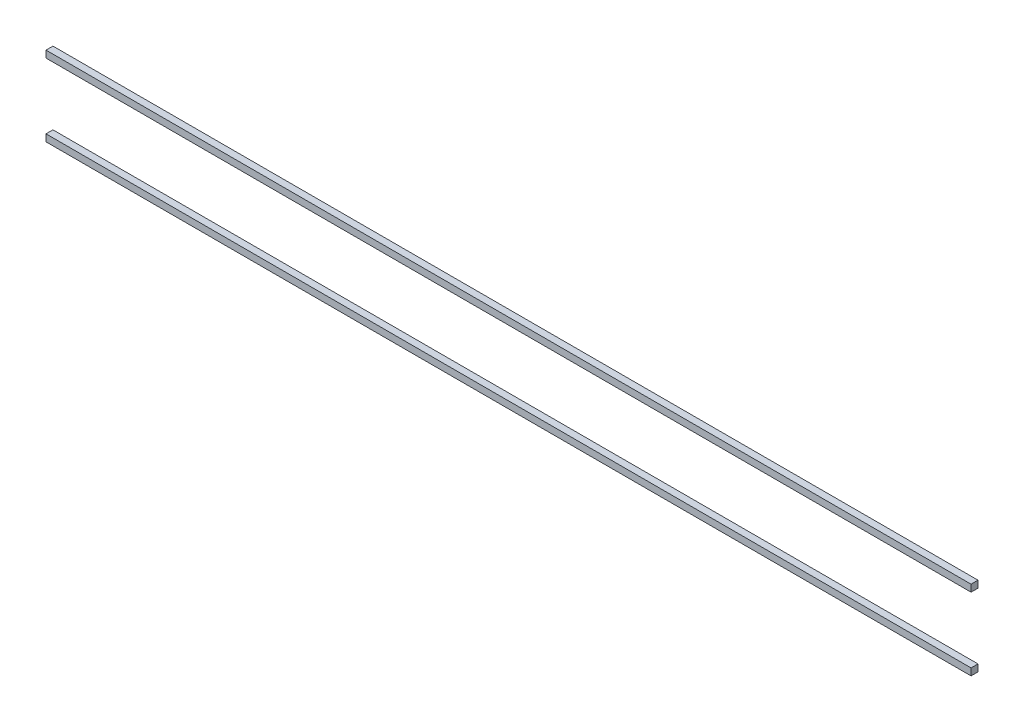
SolidWorks part; units mm, degrees
material "Balsa"
ref_plane "Front Plane" through (0, 0, 0) normal (0, 0, 1) x (1, 0, 0)
ref_plane "Top Plane" through (0, 0, 0) normal (0, 1, 0) x (1, 0, 0)
ref_plane "Right Plane" through (0, 0, 0) normal (1, 0, 0) x (0, 0, -1)
sketch "Sketch1" plane through (0, 0, 0) normal (0, 0, 1) x (1, 0, 0)
  line L0 (-18.175, 48.175) -> (18.175, 48.175)
  line L4 (405, 11.825) -> (405, 15)
  line L5 (-15, 45) -> (15, 45)
  line L7 (-15, 15) -> (15, 15)
  line L10 (405, 11.825) -> (405, 15)
  line L14 (-18.175, 11.825) -> (18.175, 11.825)
  line L16 (18.175, 48.175) -> (405, 48.175)
  line L17 (18.175, 11.825) -> (405, 11.825)
  line L18 (15, 45) -> (405, 45)
  line L19 (15, 15) -> (405, 15)
  line L20 (-18.175, 48.175) -> (-18.175, 45)
  line L21 (-18.175, 48.175) -> (-18.175, 11.825) construction
  line L22 (-15, 45) -> (-15, 15) construction
  line L23 (15, 45) -> (15, 15) construction
  line L24 (-18.175, 45) -> (-15, 45)
  line L25 (18.175, 48.175) -> (18.175, 11.825) construction
  line L26 (405, 45) -> (405, 48.175)
  line L27 (405, 45) -> (405, 48.175)
  line L28 (-18.175, 11.825) -> (-18.175, 15)
  line L29 (-18.175, 15) -> (-15, 15)
  point P4 (0, 30)
  dimension "D3" = 30
  dimension "D5" = 3.175
extrude "Boss-Extrude1" add sketch "Sketch1" along normal blind 3.175 contours L18 L26 L16 L0 L20 L24 L5 | L29 L28 L14 L17 L4 L19 L7
